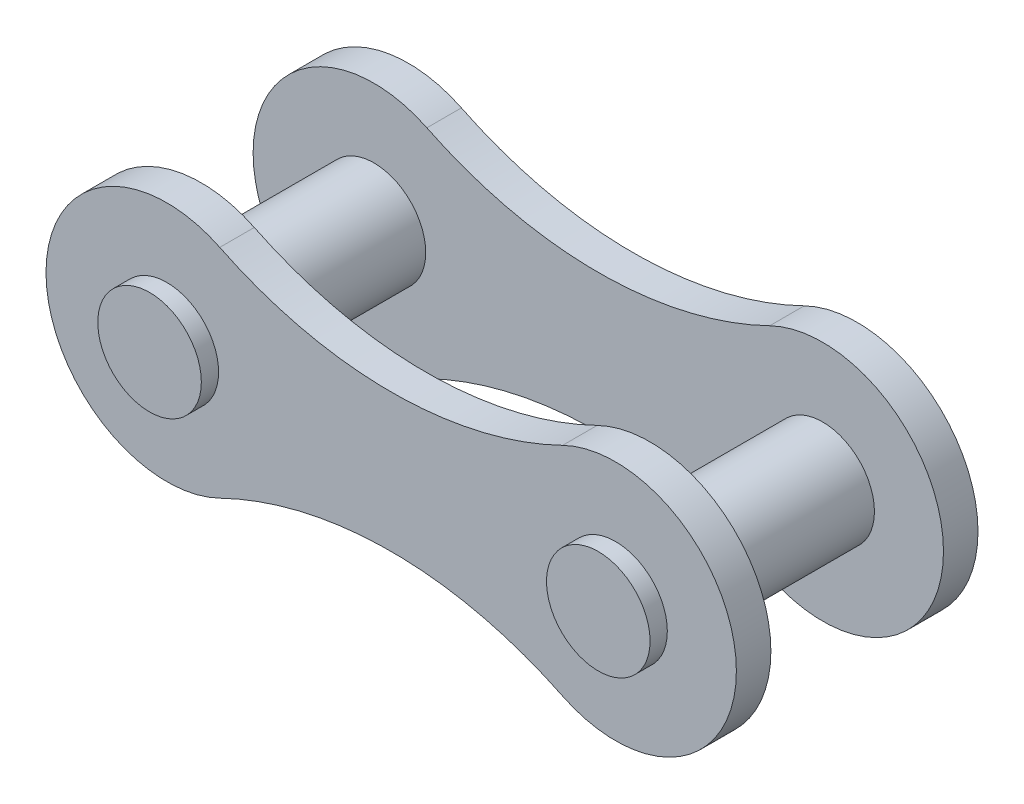
SolidWorks part; units mm, degrees
ref_plane "Alzado" through (0, 0, 0) normal (0, 0, 1) x (1, 0, 0)
ref_plane "Planta" through (0, 0, 0) normal (0, 1, 0) x (1, 0, 0)
ref_plane "Vista lateral" through (0, 0, 0) normal (1, 0, 0) x (0, 0, -1)
sketch "Croquis1" plane through (0, 0, 0) normal (0, 0, 1) x (1, 0, 0)
  line L0 (-10, 0) -> (10, 0) construction
  line L1 (0, 0) -> (0, 2.5225) construction
  line L2 (0, -2) -> (0, 2) construction
  arc A0 (4.9663, -3.1461) -> (4.9663, 3.1461) centre (6.5, 0) ccw
  arc A1 (-4.9663, -3.1461) -> (-4.9663, 3.1461) centre (-6.5, 0) cw
  arc A2 (-4.9663, 3.1461) -> (4.9663, 3.1461) centre (0, 13.3333) ccw
  arc A3 (-4.9663, -3.1461) -> (4.9663, -3.1461) centre (0, -13.3333) cw
  circle A4 centre (6.5, 0) radius 1.5
  circle A5 centre (-6.5, 0) radius 1.5
  point P4 (0, 0)
  point P9 (10, 0)
  point P14 (0, 0)
  point P17 (0, 2)
  dimension "D2" = 7
  dimension "D4" = 3
  dimension "D1" = 20
  dimension "D3" = 2
extrude "Saliente-Extruir1" add sketch "Croquis1" along normal blind 1
sketch "Croquis2" plane through (0, 0, 1) normal (0, 0, 1) x (1, 0, 0)
  circle A1 centre (-6.5, 0) radius 1.5 construction
  circle A2 centre (-6.5, 0) radius 1.5
  circle A3 centre (6.5, 0) radius 1.5 construction
  circle A4 centre (6.5, 0) radius 1.5
  dimension "D1" = 3
extrude "Saliente-Extruir2" add sketch "Croquis2" along normal blind 5 separate body
sketch "Croquis3" plane through (0, 0, 6) normal (0, 0, 1) x (1, 0, 0)
  circle A0 centre (-6.5, 0) radius 1.5 construction
  circle A1 centre (-6.5, 0) radius 1.5
  circle A2 centre (6.5, 0) radius 1.5 construction
  circle A3 centre (6.5, 0) radius 1.5
  arc A4 (-4.9663, 3.1461) -> (4.9663, 3.1461) centre (0, 13.3333) ccw
  arc A5 (-4.9663, 3.1461) -> (-4.9663, -3.1461) centre (-6.5, 0) ccw
  arc A6 (4.9663, -3.1461) -> (-4.9663, -3.1461) centre (0, -13.3333) ccw
  arc A7 (4.9663, -3.1461) -> (4.9663, 3.1461) centre (6.5, 0) ccw
  arc A8 (-4.9663, 3.1461) -> (4.9663, 3.1461) centre (0, 13.3333) ccw
  arc A9 (-4.9663, 3.1461) -> (-4.9663, -3.1461) centre (-6.5, 0) ccw
  arc A10 (4.9663, -3.1461) -> (-4.9663, -3.1461) centre (0, -13.3333) ccw
  arc A11 (4.9663, -3.1461) -> (4.9663, 3.1461) centre (6.5, 0) ccw
  dimension "D1" = 0
extrude "Saliente-Extruir4" add sketch "Croquis3" along normal blind 1 separate body
sketch "Croquis4" plane through (0, 0, 6) normal (0, 0, 1) x (1, 0, 0)
  circle A0 centre (6.5, 0) radius 1.5 construction
  circle A1 centre (-6.5, 0) radius 1.5
  circle A2 centre (-6.5, 0) radius 1.5
  circle A3 centre (6.5, 0) radius 1.5
  dimension "D1" = 0
extrude "Saliente-Extruir5" add sketch "Croquis4" along normal blind 1.5
sketch "Croquis5" plane through (0, 0, 1) normal (0, 0, -1) x (-1, 0, 0)
  circle A1 centre (-6.5, 0) radius 1.5
  circle A2 centre (-6.5, 0) radius 1.5
  circle A3 centre (6.5, 0) radius 1.5
  circle A4 centre (6.5, 0) radius 1.5
  dimension "D1" = 0
  dimension "D2" = 0
extrude "Saliente-Extruir6" add sketch "Croquis5" along normal blind 1.5
